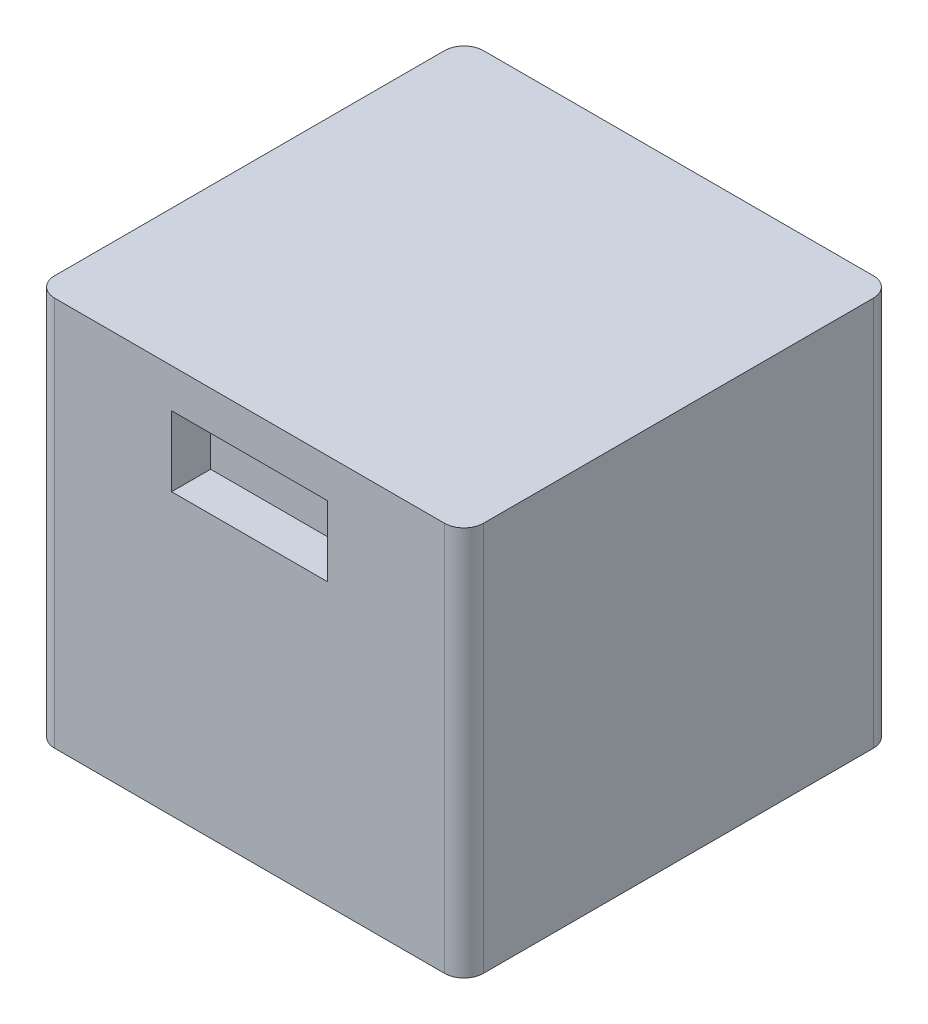
SolidWorks part; units mm, degrees
ref_plane "Front Plane" through (0, 0, 0) normal (0, 0, 1) x (1, 0, 0)
ref_plane "Top Plane" through (0, 0, 0) normal (0, 1, 0) x (1, 0, 0)
ref_plane "Right Plane" through (0, 0, 0) normal (1, 0, 0) x (0, 0, -1)
sketch "Sketch1" plane through (0, 0, 0) normal (0, 1, 0) x (1, 0, 0)
  line L1 (-110, 110) -> (110, 110)
  line L2 (-110, 110) -> (-110, -110)
  line L3 (-110, -110) -> (110, -110)
  line L4 (110, 110) -> (110, -110)
  line L5 (-110, 110) -> (110, -110) construction
  line L6 (-110, -110) -> (110, 110) construction
  point P0 (0, 0)
  dimension "D1" = 220
  dimension "D2" = 220
extrude "Boss-Extrude1" add sketch "Sketch1" along normal blind 200
fillet "Fillet1" radius 10 4 edges at (-110, 100, -110) (110, 100, -110) (110, 100, 110) (-110, 100, 110)
sketch "Sketch2" plane through (0, 0, 0) normal (0, -1, 0) x (1, 0, 0)
  line L0 (-34.8444, 0) -> (41.9716, 0) construction
  line L1 (0, 22.5696) -> (0, -60.5817) construction
  circle A0 centre (0, -50) radius 30
  circle A1 centre (0, 60) radius 30
  point P9 (0, 0)
  dimension "D2" = 60
  dimension "D4" = 60
  dimension "D1" = 50
  dimension "D3" = 60
extrude "Cut-Extrude1" cut sketch "Sketch2" against normal blind 20
sketch "Sketch3" plane through (0, 0, 110) normal (0, 0, 1) x (1, 0, 0)
  line L0 (-100, 200) -> (100, 200) construction
  line L1 (-40, 180) -> (40, 180)
  line L2 (-40, 180) -> (-40, 144)
  line L3 (-40, 144) -> (40, 144)
  line L4 (40, 180) -> (40, 144)
  line L5 (-40, 180) -> (40, 144) construction
  line L6 (-40, 144) -> (40, 180) construction
  point P0 (0, 162)
  point P5 (0, 0)
  dimension "D1" = 80
  dimension "D2" = 36
  dimension "D3" = 20
extrude "Cut-Extrude2" cut sketch "Sketch3" against normal blind 20
sketch "Sketch4" plane through (40, 0, 0) normal (-1, 0, 0) x (0, 0, 1)
  line L0 (100, 0) -> (100, 200) construction
  line L1 (93.4044, 175.9872) -> (106.5956, 175.9872)
  line L2 (93.4044, 175.9872) -> (93.4044, 152.4218)
  line L3 (93.4044, 152.4218) -> (106.5956, 152.4218)
  line L4 (106.5956, 175.9872) -> (106.5956, 152.4218)
  line L5 (93.4044, 175.9872) -> (106.5956, 152.4218) construction
  line L6 (93.4044, 152.4218) -> (106.5956, 175.9872) construction
  line L8 (90, 144) -> (110, 144) construction
  point P0 (100, 164.2045)
  dimension "D1" = 23.5654
  dimension "D2" = 13.1912
  dimension "D3" = 8.4218
extrude "Cut-Extrude3" cut sketch "Sketch4" against normal blind 10
